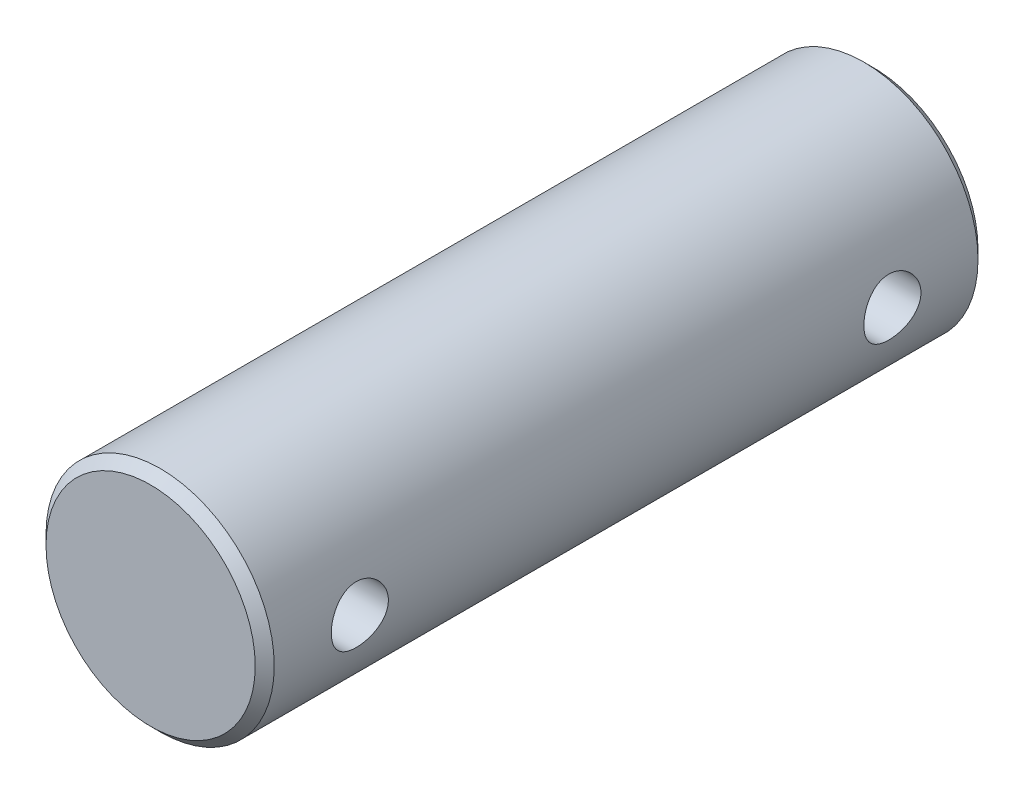
SolidWorks part; units mm, degrees
material "AISI 316 Annealed Stainless Steel Bar (SS)"
ref_plane "Front Plane" through (0, 0, 0) normal (0, 0, 1) x (1, 0, 0)
ref_plane "Top Plane" through (0, 0, 0) normal (0, 1, 0) x (1, 0, 0)
ref_plane "Right Plane" through (0, 0, 0) normal (1, 0, 0) x (0, 0, -1)
sketch "Sketch1" plane through (0, 0, 0) normal (0, 0, 1) x (1, 0, 0)
  circle A0 centre (0, 0) radius 6
  dimension "D1" = 12
extrude "Body" add sketch "Sketch1" along normal mid plane 38
sketch "Sketch2" plane through (0, 0, 0) normal (1, 0, 0) x (0, 0, -1)
  line L0 (-19, 6) -> (-19, -6) construction
  line L1 (19, -6) -> (19, 6) construction
  circle A0 centre (-14, 0) radius 1.5
  circle A1 centre (14, 0) radius 1.5
  dimension "D1" = 3
  dimension "D2" = 3
  dimension "D3" = 5
  dimension "D4" = 5
extrude "Holes" cut sketch "Sketch2" against normal through all and the other way through all
chamfer "1x 45 Chamfer" distance 0.5 angle 45 2 edges at (6, 0, -19) (6, 0, 19)
